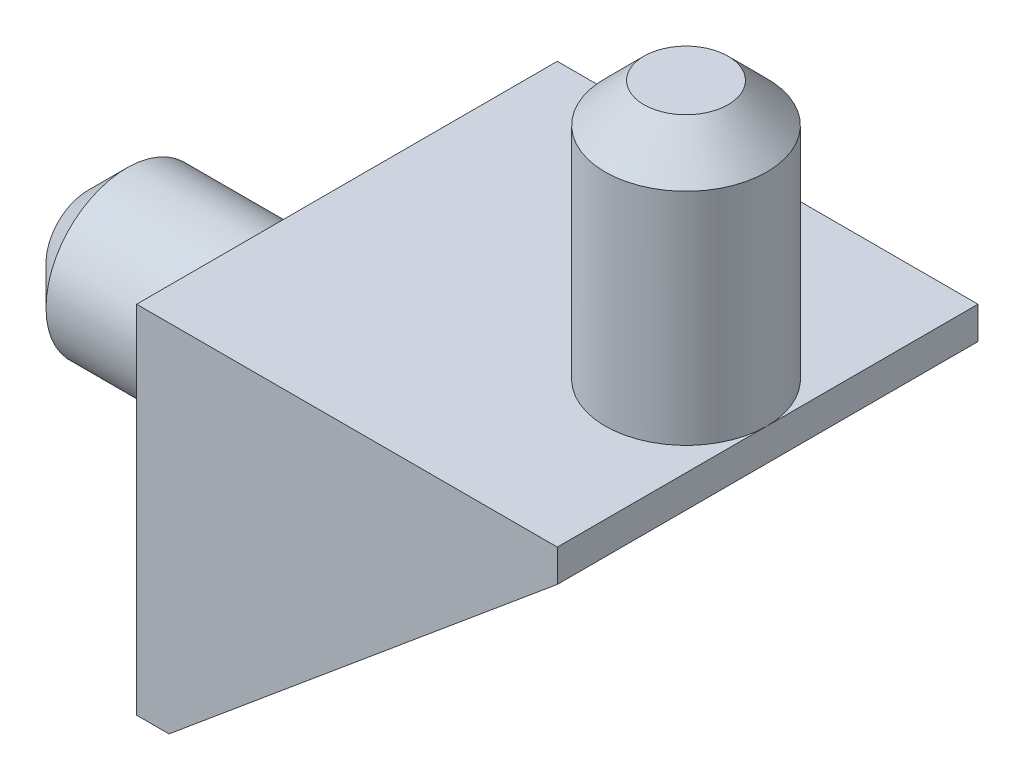
SolidWorks part; units mm, degrees
ref_plane "Front Plane" through (0, 0, 0) normal (0, 0, 1) x (1, 0, 0)
ref_plane "Top Plane" through (0, 0, 0) normal (0, 1, 0) x (1, 0, 0)
ref_plane "Right Plane" through (0, 0, 0) normal (1, 0, 0) x (0, 0, -1)
sketch "Sketch1" plane through (0, 0, 0) normal (0, 1, 0) x (1, 0, 0)
  line L1 (0, 0) -> (12, 0)
  line L2 (0, 0) -> (0, -11)
  line L3 (0, -11) -> (12, -11)
  line L4 (12, 0) -> (12, -11)
  dimension "D1" = 12
  dimension "D2" = 11
extrude "Boss-Extrude1" add sketch "Sketch1" along normal blind 1
sketch "Sketch2" plane through (0, 0, 0) normal (-1, 0, 0) x (0, 0, 1)
  line L1 (0, 1) -> (11, 1)
  line L2 (0, 1) -> (0, -10)
  line L3 (0, -10) -> (11, -10)
  line L4 (11, 1) -> (11, -10)
  dimension "D1" = 11
extrude "Boss-Extrude2" add sketch "Sketch2" along normal blind 1
sketch "Sketch3" plane through (-1, 0, 0) normal (-1, 0, 0) x (0, 0, 1)
  circle A0 centre (5.5, -4.5) radius 2.5
extrude "Boss-Extrude3" add sketch "Sketch3" along normal blind 8
chamfer "Chamfer1" distance 1.2 angle 45 1 edges at (-9, -4.5, 8)
sketch "Sketch4" plane through (0, 1, 0) normal (0, 1, 0) x (1, 0, 0)
  line L0 (12, -11) -> (12, 0) construction
  circle A0 centre (9.5, -5.523) radius 2.5
  dimension "D1" = 2.5
extrude "Boss-Extrude4" add sketch "Sketch4" along normal blind 8
chamfer "Chamfer2" distance 1.2 angle 45 1 edges at (9.5, 9, 8.023)
sketch "Sketch5" plane through (0, 0, 11) normal (0, 0, 1) x (1, 0, 0)
  line L0 (0, -10) -> (12, 0)
  line L1 (12, 0) -> (12, 1)
  line L2 (12, 1) -> (-1, 1)
  line L3 (-1, 1) -> (-1, -10)
  line L4 (-1, -10) -> (0, -10)
extrude "Boss-Extrude5" add sketch "Sketch5" along normal blind 1
sketch "Sketch6" plane through (0, 0, 0) normal (0, 0, -1) x (-1, 0, 0)
  line L0 (-12, 0) -> (0, -10)
  line L1 (0, -10) -> (1, -10)
  line L2 (1, -10) -> (1, 1)
  line L3 (1, 1) -> (-12, 1)
  line L4 (-12, 1) -> (-12, 0)
extrude "Boss-Extrude6" add sketch "Sketch6" along normal blind 1
